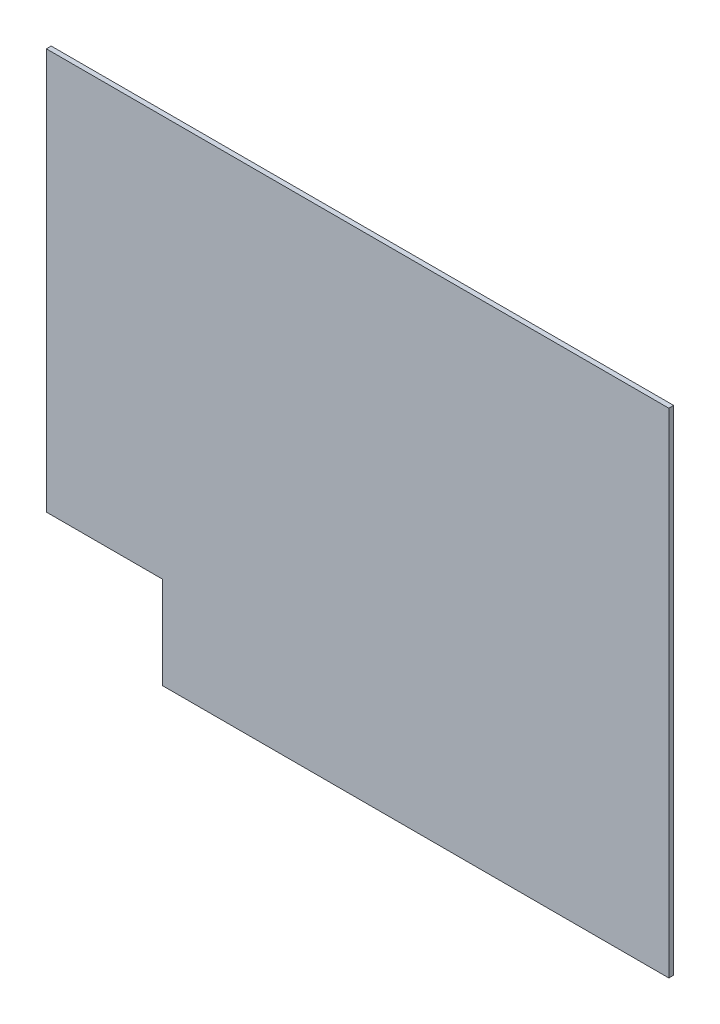
SolidWorks part; units mm, degrees
material "Acrylic (Medium-high impact)"
ref_plane "Front Plane" through (0, 0, 0) normal (0, 0, 1) x (1, 0, 0)
ref_plane "Top Plane" through (0, 0, 0) normal (0, 1, 0) x (1, 0, 0)
ref_plane "Right Plane" through (0, 0, 0) normal (1, 0, 0) x (0, 0, -1)
sketch "Sketch1" plane through (0, 0, 0) normal (0, 0, 1) x (1, 0, 0)
  line L1 (-289.5, -229.5) -> (289.5, -229.5)
  line L2 (-289.5, -229.5) -> (-289.5, 229.5)
  line L3 (-289.5, 229.5) -> (289.5, 229.5)
  line L4 (289.5, -229.5) -> (289.5, 229.5)
  line L5 (-289.5, -229.5) -> (289.5, 229.5) construction
  line L6 (-289.5, 229.5) -> (289.5, -229.5) construction
  point P0 (0, 0)
  dimension "D1" = 579
  dimension "D2" = 459
extrude "Boss-Extrude1" add sketch "Sketch1" along normal mid plane 4.4958
sketch "Sketch2" plane through (0, 0, -2.2479) normal (0, 0, -1) x (-1, 0, 0)
  line L0 (284.75, -144.2) -> (181.75, -144.2) construction
  line L1 (181.75, -224.2) -> (181.75, -144.2) construction
  line L2 (284.75, -144.2) -> (181.75, -144.2) construction
  line L3 (181.75, -224.2) -> (181.75, -144.2) construction
  line L4 (289.5, -143.7) -> (181.25, -143.7)
  line L5 (181.25, -229.5) -> (181.25, -143.7)
  line L6 (289.5, -143.7) -> (289.5, -229.5)
  line L7 (289.5, 229.5) -> (289.5, -229.5) construction
  line L8 (289.5, -229.5) -> (181.25, -229.5)
  line L9 (289.5, -229.5) -> (-289.5, -229.5) construction
  line L10 (181.25, -224.2) -> (181.25, -143.7) construction
  line L11 (284.75, -143.7) -> (181.25, -143.7) construction
  dimension "D1" = 0.5
extrude "Cut-Extrude1" cut sketch "Sketch2" against normal up to surface (4.4958 mm away) up to face at (0, 0, 2.2479)
